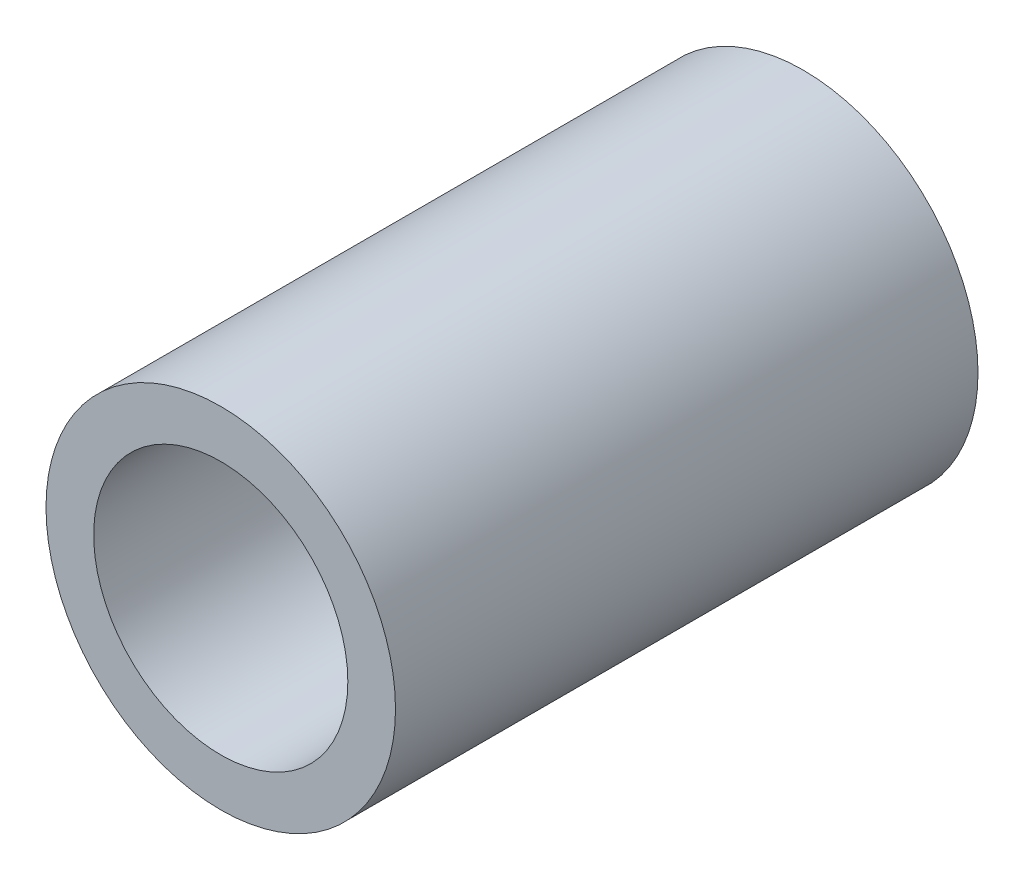
SolidWorks part; units mm, degrees
ref_plane "Front Plane" through (0, 0, 0) normal (0, 0, 1) x (1, 0, 0)
ref_plane "Top Plane" through (0, 0, 0) normal (0, 1, 0) x (1, 0, 0)
ref_plane "Right Plane" through (0, 0, 0) normal (1, 0, 0) x (0, 0, -1)
sketch "Sketch2" plane through (0, 0, 0) normal (0, 0, 1) x (1, 0, 0)
  circle A0 centre (0, 0) radius 2.1818
  circle A1 centre (0, 0) radius 3
  dimension "D1" = 6
extrude "Boss-Extrude1" add sketch "Sketch2" along normal blind 10
